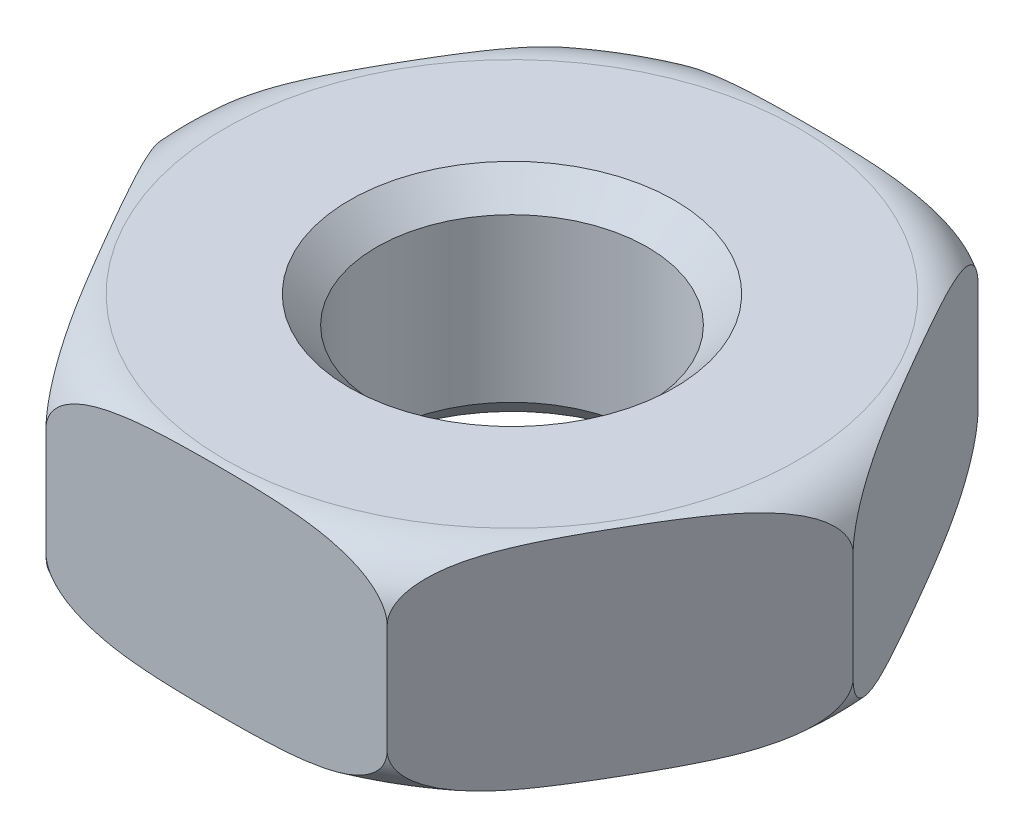
SolidWorks part; units mm, degrees
ref_plane "Front Plane" through (0, 0, 0) normal (0, 0, 1) x (1, 0, 0)
ref_plane "Top Plane" through (0, 0, 0) normal (0, 1, 0) x (1, 0, 0)
ref_plane "Right Plane" through (0, 0, 0) normal (1, 0, 0) x (0, 0, -1)
sketch "Sketch1" plane through (0, 0, 0) normal (0, 1, 0) x (1, 0, 0)
  line L1 (-1.575, 2.728) -> (-3.15, 0)
  line L2 (-3.15, 0) -> (-1.575, -2.728)
  line L3 (-1.575, -2.728) -> (1.575, -2.728)
  line L4 (1.575, -2.728) -> (3.15, 0)
  line L5 (3.15, 0) -> (1.575, 2.728)
  line L6 (1.575, 2.728) -> (-1.575, 2.728)
  circle A0 centre (0, 0) radius 2.728 construction
  circle A1 centre (0, 0) radius 1.25
  dimension "D2" = 2.5
  dimension "D1" = 6.3
extrude "Boss-Extrude1" add sketch "Sketch1" along normal mid plane 2
chamfer "Chamfer1" distance 0.25 angle 45 2 edges at (0, 1, 1.25) (0, -1, 1.25)
sketch "Sketch3" plane through (0, 0, 0) normal (0, 0, 1) x (1, 0, 0)
  line L0 (3.15, 1) -> (3.15, -1) construction
  line L1 (1.575, 1) -> (3.15, 1) construction
  line L2 (2.65, 1) -> (3.15, 1)
  line L3 (3.15, 1) -> (3.15, 0.5)
  arc A0 (3.15, 0.5) -> (2.65, 1) centre (2.65, 0.5) ccw
  dimension "D1" = 0.5
revolve "Cut-Revolve1" cut sketch "Sketch3" angle 360 about axis through (0, 1, 0) along (0, -1, 0)
mirror "Mirror1" about plane through (0, 0, 0) normal (0, 1, 0) of "Cut-Revolve1"
